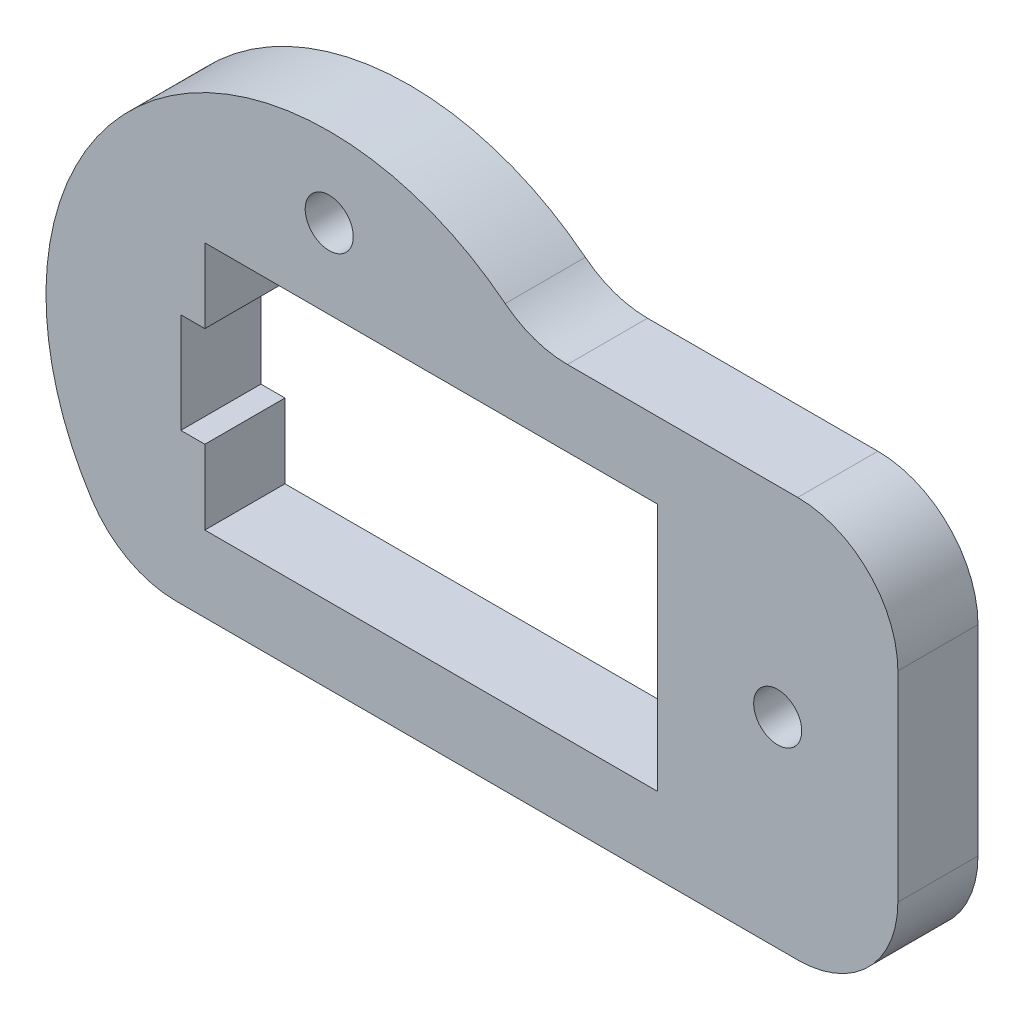
SolidWorks part; units mm, degrees
ref_plane "Front Plane" through (0, 0, 0) normal (0, 0, 1) x (1, 0, 0)
ref_plane "Top Plane" through (0, 0, 0) normal (0, 1, 0) x (1, 0, 0)
ref_plane "Right Plane" through (0, 0, 0) normal (1, 0, 0) x (0, 0, -1)
sketch "Sketch1" plane through (0, 0, 0) normal (0, 0, 1) x (1, 0, 0)
  line L1 (0, 20) -> (38.39, 20)
  line L2 (38.39, 20) -> (38.39, 0)
  line L3 (38.39, 0) -> (0, 0)
  line L4 (0, 20) -> (0, 0)
  line L5 (3.79, 16.21) -> (26.39, 16.21)
  line L6 (3.79, 16.21) -> (3.79, 3.79)
  line L7 (3.79, 3.79) -> (26.39, 3.79)
  line L8 (26.39, 16.21) -> (26.39, 3.79)
  line L9 (10, 16.21) -> (10, 24.1421) construction
  line L10 (3.79, 12.5) -> (2.59, 12.5)
  line L11 (3.79, 12.5) -> (3.79, 7.5)
  line L12 (3.79, 7.5) -> (2.59, 7.5)
  line L13 (2.59, 12.5) -> (2.59, 7.5)
  circle A3 centre (10, 10) radius 6.21
  circle A4 centre (10, 10) radius 1.5
  arc A5 (15.5221, 12.8409) -> (15.5221, 7.1591) centre (15.75, 10) cw
  circle A6 centre (10, 10) radius 14.1421
  circle A10 centre (32.39, 10) radius 1.2
  circle A12 centre (10, 20.1761) radius 1.2
  point P0 (3.79, 10)
  point P13 (0, 10)
  point P23 (3.19, 12.5)
  point P24 (2.59, 10)
  point P28 (10, 20.1761)
  point P33 (26.39, 10)
  dimension "D4" = 5.75
  dimension "D5" = 3
  dimension "D6" = 2.85
  dimension "D9" = 1.2
  dimension "D11" = 12
  dimension "D3" = 2.4
  dimension "D1" = 22.6
  dimension "D2" = 12.42
  dimension "D7" = 10
  dimension "D8" = 10
  dimension "D10" = 5
  dimension "D12" = 6
extrude "Boss-Extrude1" add sketch "Sketch1" along normal blind 4
fillet "Fillet1" radius 5 4 edges at (0, 0, 2) (38.39, 0, 2) (38.39, 20, 2) (20, 20, 2)
equation "\"D3\"=3.46607"
